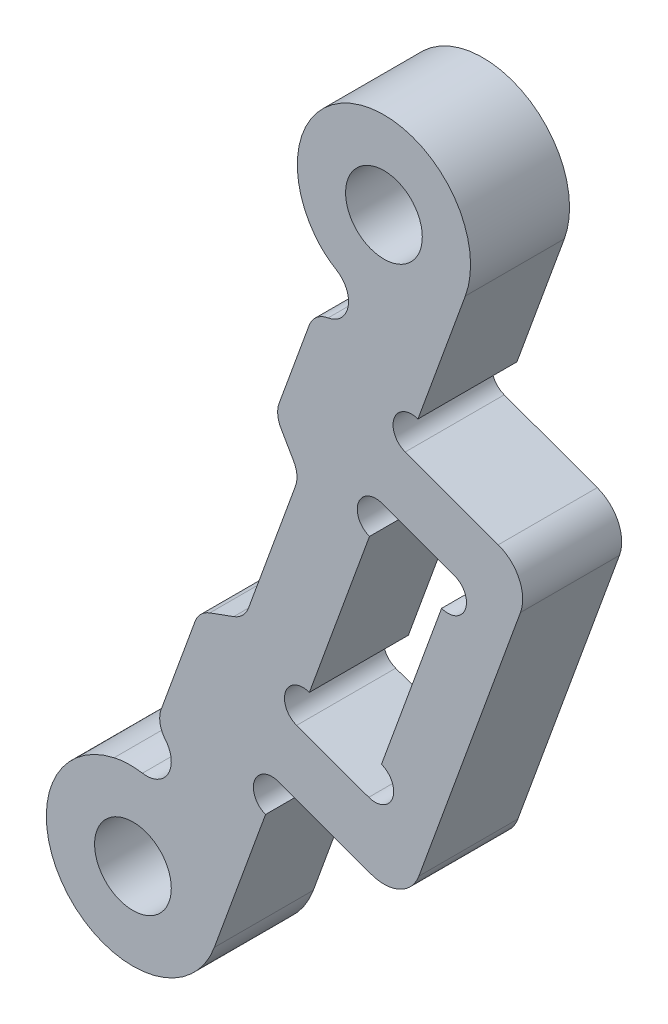
SolidWorks part; units mm, degrees
ref_plane "前视基准面" through (0, 0, 0) normal (0, 0, 1) x (1, 0, 0)
ref_plane "上视基准面" through (0, 0, 0) normal (0, 1, 0) x (1, 0, 0)
ref_plane "右视基准面" through (0, 0, 0) normal (1, 0, 0) x (0, 0, -1)
sketch "草图1" plane through (0, 0, 0) normal (0, 0, 1) x (1, 0, 0)
  line L0 (-17.5, 11) -> (-10, 11)
  line L1 (17.5, -7.5) -> (-17.5, -7.5) construction
  line L2 (17.5, -7.5) -> (17.5, 7.5) construction
  line L3 (17.5, 7.5) -> (-17.5, 7.5) construction
  line L4 (-17.5, -7.5) -> (-17.5, 7.5) construction
  line L5 (17.5, -7.5) -> (-17.5, 7.5) construction
  line L6 (17.5, 7.5) -> (-17.5, -7.5) construction
  line L7 (-10, 11) -> (-8.3218, 9)
  line L8 (-8.3218, 9) -> (8.3218, 9)
  line L9 (8.3218, 9) -> (10, 11)
  line L10 (10, 11) -> (17.5, 11)
  line L11 (-14.0777, -8.2333) -> (-2.3046, -10.7559)
  line L12 (-17.6552, 10.9966) -> (-37, 10.1377)
  line L13 (14.0777, -8.2333) -> (2.3046, -10.7559)
  line L14 (-37, 10.1377) -> (-28.9425, -12)
  line L15 (-28.9425, -12) -> (-17.1992, -10.9871)
  line L16 (17.6552, 10.9966) -> (37, 10.1377)
  line L17 (37, 10.1377) -> (28.9425, -12)
  line L18 (28.9425, -12) -> (17.1992, -10.9871)
  line L19 (-37, 10.1377) -> (-38.9566, 15.5135) construction
  line L20 (-38.9566, 15.5135) -> (-41.7757, 14.4874) construction
  line L21 (-41.7757, 14.4874) -> (-29.805, -18.4018) construction
  line L22 (-29.805, -18.4018) -> (-26.9859, -17.3758) construction
  line L23 (-26.9859, -17.3758) -> (-28.9425, -12) construction
  line L28 (-38.6034, 5.7716) -> (-48.0003, 2.3514) construction
  line L29 (-32.447, -11.1429) -> (-41.844, -14.5631) construction
  line L30 (-48.0003, 2.3514) -> (-41.844, -14.5631) construction
  line L31 (-41.844, -14.5631) -> (-44.663, -15.5892) construction
  line L32 (-44.663, -15.5892) -> (-50.8194, 1.3253) construction
  line L33 (-50.8194, 1.3253) -> (-48.0003, 2.3514) construction
  line L34 (-51.5, -8.5) -> (-44.9222, -6.1059) construction
  line L35 (0, 9) -> (0, -11) construction
  line L36 (41.7757, 14.4874) -> (29.805, -18.4018) construction
  line L37 (37, 10.1377) -> (38.9566, 15.5135) construction
  line L38 (38.9566, 15.5135) -> (41.7757, 14.4874) construction
  line L39 (50.8194, 1.3253) -> (48.0003, 2.3514) construction
  line L40 (38.6034, 5.7716) -> (48.0003, 2.3514) construction
  line L41 (44.663, -15.5892) -> (50.8194, 1.3253) construction
  line L42 (41.844, -14.5631) -> (44.663, -15.5892) construction
  line L43 (48.0003, 2.3514) -> (41.844, -14.5631) construction
  line L44 (32.447, -11.1429) -> (41.844, -14.5631) construction
  line L45 (26.9859, -17.3758) -> (28.9425, -12) construction
  line L46 (29.805, -18.4018) -> (26.9859, -17.3758) construction
  line L47 (44.9222, -6.1059) -> (32.7061, -1.6596) construction
  circle A0 centre (0, 0) radius 7
  circle A2 centre (17.5, 7.5) radius 1.55
  circle A3 centre (17.5, -7.5) radius 1.55
  circle A4 centre (-17.5, -7.5) radius 1.55
  circle A5 centre (-17.5, 7.5) radius 1.55
  arc A6 (-17.5, 11) -> (-17.6552, 10.9966) centre (-17.5, 7.5) ccw
  arc A7 (-17.1992, -10.9871) -> (-14.0777, -8.2333) centre (-17.5, -7.5) ccw
  arc A8 (14.0777, -8.2333) -> (17.1992, -10.9871) centre (17.5, -7.5) ccw
  arc A9 (17.6552, 10.9966) -> (17.5, 11) centre (17.5, 7.5) ccw
  arc A10 (-2.3046, -10.7559) -> (2.3046, -10.7559) centre (0, 0) ccw
  circle A11 centre (-51.5, -8.5) radius 4 construction
  circle A12 centre (51.5, -8.5) radius 4 construction
  dimension "D1" = 14
  dimension "D2" = 11
  dimension "D4" = 3.1
  dimension "D6" = 7
  dimension "D18" = 8
  dimension "D19" = 8.5
  dimension "D10" = 103
  dimension "D3" = 35
  dimension "D5" = 15
  dimension "D7" = 2
  dimension "D8" = 20
  dimension "D9" = 50
  dimension "D11" = 70
  dimension "D12" = 74
  dimension "D13" = 12
  dimension "D14" = 3
  dimension "D15" = 10
  dimension "D16" = 18
  dimension "D17" = 3
  dimension "D20" = 35
extrude "凸台-拉伸1" add sketch "草图1" along normal mid plane 4
fillet "圆角1" radius 1 2 edges at (14.0777, -8.2333, 0) (-14.0777, -8.2333, 0)
sketch "草图2" plane through (0, 0, 2) normal (0, 0, 1) x (1, 0, 0)
  line L0 (-20.5, 7.8673) -> (-32.7826, 7.322)
  line L1 (-32.7826, 7.322) -> (-27.2229, -7.9533)
  line L2 (-27.2229, -7.9533) -> (-20.5, 7.8673)
  line L3 (-19.2518, 4.4123) -> (-24.5732, -8.1101)
  line L4 (-24.5732, -8.1101) -> (-21.0369, -7.8051)
  line L5 (-19.1827, -4.3741) -> (-15.3311, 4.6896)
  line L6 (-17.6552, 10.9966) -> (-37, 10.1377) construction
  line L7 (-37, 10.1377) -> (-28.9425, -12) construction
  line L8 (-28.9425, -12) -> (-17.1992, -10.9871) construction
  arc A0 (-21.0369, -7.8051) -> (-19.1827, -4.3741) centre (-17.5, -7.5) cw
  circle A1 centre (-17.5, -7.5) radius 1.55 construction
  arc A2 (-19.2518, 4.4123) -> (-15.3311, 4.6896) centre (-17.5, 7.5) ccw
  circle A3 centre (-17.5, 7.5) radius 1.55 construction
  circle A4 centre (-17.5, 7.5) radius 1.55 construction
  dimension "D1" = 2
  dimension "D2" = 2
  dimension "D6" = 3.5
  dimension "D7" = 3
  dimension "D3" = 3
  dimension "D4" = 3
  dimension "D5" = 2.5
extrude "切除-拉伸1" cut sketch "草图2" against normal through all both and the other way through all
fillet "圆角2" radius 1 8 edges at (-19.2518, 4.4123, 0) (-21.0369, -7.8051, 0) (-19.1827, -4.3741, 0) (-15.3311, 4.6896, 0) (-24.5732, -8.1101, 0) (-27.2229, -7.9533, 0) (-32.7826, 7.322, 0) (-20.5, 7.8673, 0)
mirror "镜向1" about plane through (0, 0, 0) normal (1, 0, 0) of "圆角2", "切除-拉伸1"
sketch "草图3" plane through (0, 0, 2) normal (0, 0, 1) x (1, 0, 0)
  line L0 (-17.6552, 10.9966) -> (-37, 10.1377) construction
  line L1 (-37, 10.1377) -> (-28.9425, -12) construction
  line L2 (-28.9425, -12) -> (-17.1992, -10.9871) construction
  line L3 (-37.6991, 12.0585) -> (-37, 10.1377)
  line L4 (-37, 10.1377) -> (-32.4761, 10.3385)
  line L5 (-27.5576, -15.8051) -> (-28.9425, -12)
  line L6 (-28.9425, -12) -> (-22.7304, -11.4642)
  circle A0 centre (-34.4102, 13.2556) radius 1.55
  circle A1 centre (-24.2687, -14.608) radius 1.55
  arc A2 (-32.4761, 10.3385) -> (-37.6991, 12.0585) centre (-34.4102, 13.2556) ccw
  arc A3 (-27.5576, -15.8051) -> (-22.7304, -11.4642) centre (-24.2687, -14.608) ccw
  dimension "D1" = 3.1
  dimension "D2" = 3
  dimension "D3" = 7
  dimension "D4" = 3
extrude "凸台-拉伸2" add sketch "草图3" against normal up to surface (4 mm away) up to face at (26.873, 2.7167, -2)
mirror "镜向2" about plane through (0, 0, 0) normal (1, 0, 0) of "凸台-拉伸2"
fillet "圆角3" radius 1 4 edges at (-22.7304, -11.4642, 0) (-32.4761, 10.3385, 0) (32.4761, 10.3385, 0) (22.7304, -11.4642, 0)
sketch "草图4" plane through (0, 0, 2) normal (0, 0, 1) x (1, 0, 0)
  line L0 (-16.3849, -4.1824) -> (-12.0579, 6)
  line L1 (-12.0579, 6) -> (-8, 6)
  line L2 (-15.1087, -4.9443) -> (-7.5429, -6.5654)
  line L3 (-13.2099, -8.4192) -> (-2.3046, -10.7559) construction
  line L4 (8.3218, 9) -> (-8.3218, 9) construction
  line L5 (-19.0548, -4.0732) -> (-16.2308, 2.5723) construction
  arc A0 (-8, 6) -> (-7.5429, -6.5654) centre (0, 0) ccw
  circle A1 centre (0, 0) radius 7 construction
  arc A2 (-15.1087, -4.9443) -> (-16.3849, -4.1824) centre (-17.5, -7.5) ccw
  dimension "D1" = 3
  dimension "D2" = 2.5
  dimension "D3" = 3
  dimension "D4" = 3
extrude "切除-拉伸2" cut sketch "草图4" against normal through all
mirror "镜向3" about plane through (0, 0, 0) normal (1, 0, 0) of "切除-拉伸2"
fillet "圆角4" radius 1 10 edges at (-12.0579, 6, 0) (-8, 6, 0) (-7.5429, -6.5654, 0) (-15.1087, -4.9443, 0) (-16.3849, -4.1824, 0) (8, 6, 0) (12.0579, 6, 0) (16.3849, -4.1824, 0) (15.1087, -4.9443, 0) (7.5429, -6.5654, 0)
sketch "草图5" plane through (0, 0, 2) normal (0, 0, 1) x (1, 0, 0)
  line L0 (44.9222, -6.1059) -> (32.7061, -1.6596) construction
  line L1 (30.885, -6.3708) -> (33.798, -7.4311)
  line L2 (30.885, -6.3708) -> (34.3394, 3.1201)
  line L3 (34.3394, 3.1201) -> (37.2524, 2.0598)
  line L4 (33.798, -7.4311) -> (37.2524, 2.0598)
  line L5 (30.885, -6.3708) -> (37.2524, 2.0598) construction
  line L6 (34.3394, 3.1201) -> (33.798, -7.4311) construction
  line L7 (37, 10.1377) -> (28.9425, -12) construction
  point P0 (34.0687, -2.1555)
  dimension "D1" = 3
  dimension "D2" = 3.1
  dimension "D3" = 10.1
extrude "切除-拉伸3" cut sketch "草图5" against normal through all
sketch "草图7" plane through (0, 0, 2) normal (0, 0, 1) x (1, 0, 0)
  line L0 (35.2713, 5.3881) -> (40.4396, 3.507)
  line L1 (34.4333, 3.0859) -> (37.6991, 12.0585) construction
  line L2 (40.4396, 3.507) -> (35.3093, -10.5884)
  line L3 (35.3093, -10.5884) -> (30.141, -8.7073)
  line L4 (27.5576, -15.8051) -> (30.9789, -6.405) construction
  line L5 (30.141, -8.7073) -> (30.9789, -6.405)
  line L6 (30.9789, -6.405) -> (33.798, -7.4311)
  line L7 (33.798, -7.4311) -> (37.2524, 2.0598)
  line L8 (37.2524, 2.0598) -> (34.4333, 3.0859)
  line L9 (34.4333, 3.0859) -> (35.2713, 5.3881)
  dimension "D1" = 15
  dimension "D2" = 2.5
extrude "凸台-拉伸3" add sketch "草图7" against normal up to surface (4 mm away)
mirror "镜向4" about plane through (0, 0, 0) normal (1, 0, 0) of "凸台-拉伸3", "切除-拉伸3"
sketch "草图8" plane through (0, 0, -2) normal (0, 0, -1) x (-1, 0, 0)
  line L0 (-33.798, -7.4311) -> (-37.2524, 2.0598) construction
  line L1 (-34.3394, 3.1201) -> (-30.885, -6.3708) construction
  line L2 (-35.2713, 5.3881) -> (-37.6991, 12.0585) construction
  line L3 (-27.5576, -15.8051) -> (-30.141, -8.7073) construction
  circle A0 centre (-36.9959, 1.355) radius 0.75
  circle A1 centre (-34.0829, 2.4153) radius 0.75
  circle A2 centre (-34.0545, -6.7263) radius 0.75
  circle A3 centre (-31.1415, -5.6661) radius 0.75
  circle A4 centre (-35.5278, 6.0929) radius 0.75
  circle A5 centre (-29.8845, -9.4121) radius 0.75
  dimension "D1" = 1.5
extrude "切除-拉伸4" cut sketch "草图8" against normal through all
mirror "镜向5" about plane through (0, 0, 0) normal (1, 0, 0) of "切除-拉伸4"
fillet "圆角5" radius 1.5 4 edges at (40.4396, 3.507, 0) (35.3093, -10.5884, 0) (-40.4396, 3.507, 0) (-35.3093, -10.5884, 0)
sketch "草图9" plane through (0, 0, -2) normal (0, 0, -1) x (-1, 0, 0)
  line L0 (-32.3165, 6.0414) -> (-33.6953, 9.8294)
  line L1 (-32.3165, 6.0414) -> (-28.0907, -5.5691) construction
  line L2 (-34.4102, 16.7556) -> (45.5898, 16.7556)
  line L3 (45.5898, 16.7556) -> (45.5898, -18.108)
  line L4 (45.5898, -18.108) -> (-24.2687, -18.108)
  line L5 (-28.0907, -5.5691) -> (-25.9233, -11.5238)
  line L6 (-32.3165, 6.0414) -> (-28.0907, -5.5691)
  arc A0 (-33.6953, 9.8294) -> (-34.4102, 16.7556) centre (-34.4102, 13.2556) ccw
  arc A2 (-31.209, 11.8406) -> (-37.6991, 12.0585) centre (-34.4102, 13.2556) ccw construction
  arc A3 (-27.5576, -15.8051) -> (-21.2787, -12.7887) centre (-24.2687, -14.608) ccw construction
  arc A4 (-24.2687, -18.108) -> (-25.9233, -11.5238) centre (-24.2687, -14.608) ccw
  dimension "D1" = 80
extrude "切除-拉伸5" cut sketch "草图9" against normal through all
sketch "草图10" plane through (0, 0, -2) normal (0, 0, -1) x (-1, 0, 0)
  line L0 (-32.3234, 10.4458) -> (-24.4762, -11.1141)
  line L1 (-33.6953, 9.8294) -> (-25.9233, -11.5238) construction
  line L2 (-33.6953, 9.8294) -> (-25.9233, -11.5238)
  arc A0 (-33.6953, 9.8294) -> (-37.6991, 12.0585) centre (-34.4102, 13.2556) ccw construction
  arc A1 (-27.5576, -15.8051) -> (-25.9233, -11.5238) centre (-24.2687, -14.608) ccw construction
  arc A2 (-33.6953, 9.8294) -> (-32.3234, 10.4458) centre (-34.4102, 13.2556) ccw
  arc A3 (-24.4762, -11.1141) -> (-25.9233, -11.5238) centre (-24.2687, -14.608) ccw
  dimension "D1" = 1.5
extrude "凸台-拉伸4" add sketch "草图10" against normal up to surface (4 mm away) up to face at (32.8602, 13.2556, 2)
sketch "草图11" plane through (0, 0, -2) normal (0, 0, -1) x (-1, 0, 0)
  line L0 (-30.0166, 4.1081) -> (-30.9957, 2.4123)
  line L1 (-24.4762, -11.1141) -> (-32.3234, 10.4458) construction
  line L2 (-30.9957, 2.4123) -> (-28.7785, -3.6794)
  line L3 (-28.7785, -3.6794) -> (-26.9384, -4.3491)
  line L4 (-26.9384, -4.3491) -> (-30.0166, 4.1081)
  line L5 (-32.6122, -1.6254) -> (-28.4775, -0.1205) construction
  line L6 (-33.8263, 1.7105) -> (-31.398, -4.9613) construction
  dimension "D1" = 1.5
  dimension "D2" = 9
  dimension "D3" = 50
extrude "切除-拉伸6" cut sketch "草图11" against normal through all
sketch "草图12" plane through (0, 0, -2) normal (0, 0, -1) x (-1, 0, 0)
  line L0 (-30.0166, 4.1081) -> (-32.3234, 10.4458) construction
  line L1 (-24.4762, -11.1141) -> (-26.9384, -4.3491) construction
  circle A0 centre (-31.9813, 9.5061) radius 1
  circle A1 centre (-24.8182, -10.1744) radius 1
  dimension "D1" = 2
extrude "切除-拉伸7" cut sketch "草图12" against normal through all
fillet "圆角6" radius 3 2 edges at (24.4762, -11.1141, 0) (32.3234, 10.4458, 0)
fillet "圆角7" radius 1 2 edges at (28.7785, -3.6794, 0) (30.9957, 2.4123, 0)
fillet "圆角8" radius 1 4 edges at (26.9384, -4.3491, 0) (25.1602, -9.2348, 0) (31.6393, 8.5664, 0) (30.0166, 4.1081, 0)
